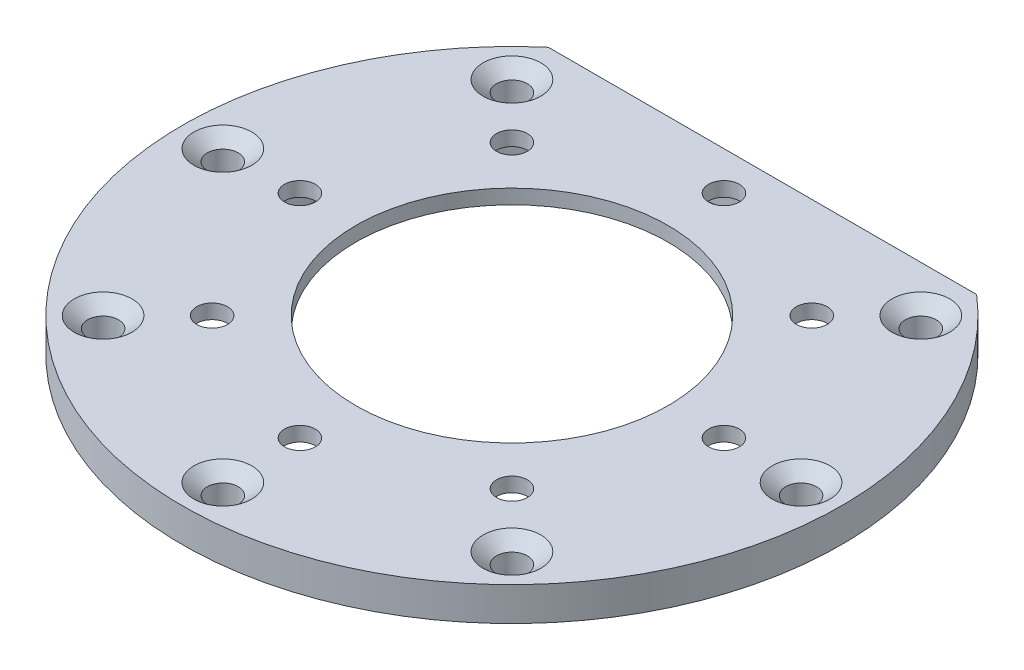
SolidWorks part; units mm, degrees
ref_plane "Front Plane" through (0, 0, 0) normal (0, 0, 1) x (1, 0, 0)
ref_plane "Top Plane" through (0, 0, 0) normal (0, 1, 0) x (1, 0, 0)
ref_plane "Right Plane" through (0, 0, 0) normal (1, 0, 0) x (0, 0, -1)
ref_axis "Axe2" through (0, 37.3734, 0) along (0, -1, 0)
sketch "Esquisse2" plane through (0, 0, 0) normal (0, 0, 1) x (1, 0, 0)
  line L0 (34.2, 0) -> (34.2, 3.5)
  line L3 (34.2, 3.5) -> (16.2, 3.5)
  line L4 (16.2, 3.5) -> (16.2, 2)
  line L5 (24.2, 0) -> (34.2, 0)
  line L6 (16.2, 2) -> (24.2, 2)
  line L7 (24.2, 2) -> (24.2, 0)
  dimension "D1" = 24.2
  dimension "D2" = 10
  dimension "D3" = 16.2
  dimension "D4" = 2
  dimension "D5" = 1.5
revolve "Révolution1" add sketch "Esquisse2" angle 360 about axis through (0, 37.3734, 0) along (0, -1, 0)
sketch "Esquisse3" plane through (0, 3.5, 0) normal (0, 1, 0) x (1, 0, 0)
  circle A0 centre (22, 0) radius 1.6
  dimension "D1" = 3.2
  dimension "D2" = 22
extrude "Enlèv. mat.-Extru.1" cut sketch "Esquisse3" against normal through all
hole_wizard "Fraisage pour vis à tête fraisée (100) #01" positions "Esquisse4" profile "Esquisse5" countersink size "#0" standard "Ansi Inch" end condition through all
sketch "Esquisse4" plane through (0, 3.5, 0) normal (0, 1, 0) x (1, 0, 0)
  point P0 (30, 0)
  dimension "D1" = 30
sketch "Esquisse5" plane through (30, 3.5, 0) normal (1, 0, 0) x (0, 0, 1)
  line L0 (0, 0) -> (0, 3.5)
  line L1 (0, 3.5) -> (1.6, 3.5)
  line L2 (1.6, 3.5) -> (1.6, 1.1747)
  line L3 (1.6, 1.1747) -> (3, 0)
  line L5 (3, 0) -> (0, 0)
  line L6 (-1.6, 1.1747) -> (-3, 0) construction
  line L11 (0, -6.35) -> (0, 107.95) construction
  dimension "Diamètre du perçage jusqu'au prochain" = 3.2
  dimension "Profondeur du perçage jusqu'au prochain" = 3.5
  dimension "Diamètre du fraisage entrant" = 6
  dimension "Angle du fraisage entrant" = 100
pattern_circular "Répétition circulaire1" count 8 every 45 about axis through (0, 0, 0) along (0, 1, 0) of "Fraisage pour vis à tête fraisée (100) #01", "Enlèv. mat.-Extru.1"
sketch "Sketch1" plane through (0, 0, 0) normal (0, -1, 0) x (-1, 0, 0)
  line L1 (22.218, 26) -> (-22.218, 26)
  line L2 (22.218, 26) -> (22.218, 34.2)
  line L3 (22.218, 34.2) -> (-22.218, 34.2)
  line L4 (-22.218, 26) -> (-22.218, 34.2)
  circle A0 centre (0, 0) radius 34.2 construction
  point P6 (-22.2389, 25.9822)
  dimension "D1" = 26
extrude "Cut-Extrude1" cut sketch "Sketch1" against normal through all
